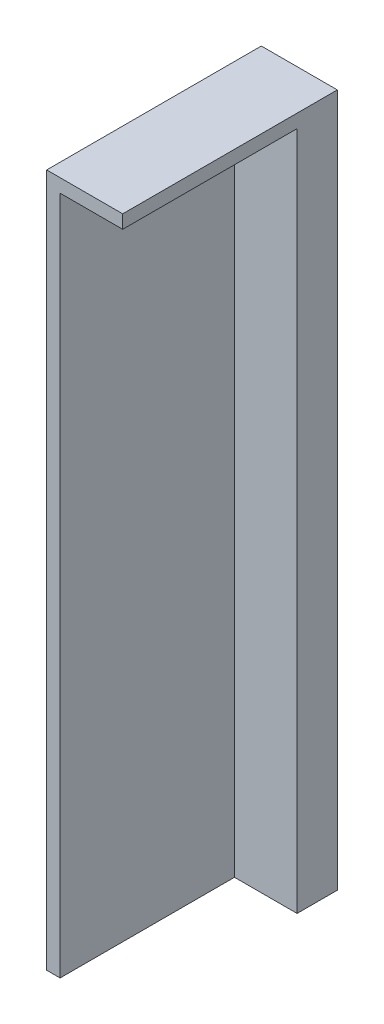
SolidWorks part; units mm, degrees
ref_plane "Front Plane" through (0, 0, 0) normal (0, 0, 1) x (1, 0, 0)
ref_plane "Top Plane" through (0, 0, 0) normal (0, 1, 0) x (1, 0, 0)
ref_plane "Right Plane" through (0, 0, 0) normal (1, 0, 0) x (0, 0, -1)
sketch "Sketch1" plane through (0, 0, 0) normal (0, 0, 1) x (1, 0, 0)
  line L0 (0, 0) -> (2605.2992, 0) construction
  line L1 (0, 0) -> (0, -2605.2992) construction
  line L3 (-2.125, 19.375) -> (2.125, 19.375)
  line L4 (-2.125, 19.375) -> (-2.125, -19.375)
  line L5 (-2.125, -19.375) -> (2.125, -19.375)
  line L6 (2.125, 19.375) -> (2.125, -19.375)
  point P9 (0, 19.375)
  point P10 (2.125, 0)
  dimension "D1" = 4.25
  dimension "D2" = 38.75
extrude "Boss-Extrude1" add sketch "Sketch1" along normal blind 12
sketch "Sketch2" plane through (-2.125, 0, 0) normal (-1, 0, 0) x (0, 0, 1)
  line L0 (12, 19.375) -> (0, 19.375) construction
  line L1 (12, -19.375) -> (2.25, -19.375)
  line L2 (12, -19.375) -> (12, 18.625)
  line L3 (12, 18.625) -> (2.25, 18.625)
  line L4 (2.25, -19.375) -> (2.25, 18.625)
  line L5 (0, 19.375) -> (0, -19.375) construction
  dimension "D1" = 0.75
  dimension "D2" = 2.25
extrude "Cut-Extrude1" cut sketch "Sketch2" against normal blind 3.5
ref_plane "Plane1" through (-12.125, 0, 0) normal (-1, 0, 0) x (0, 0, 1)
mirror "Mirror2" about plane through (-12.125, 0, 0) normal (-1, 0, 0) of bodies 104
delete or keep bodies "Body-Delete/Keep 1" type delete bodies bodies 104
